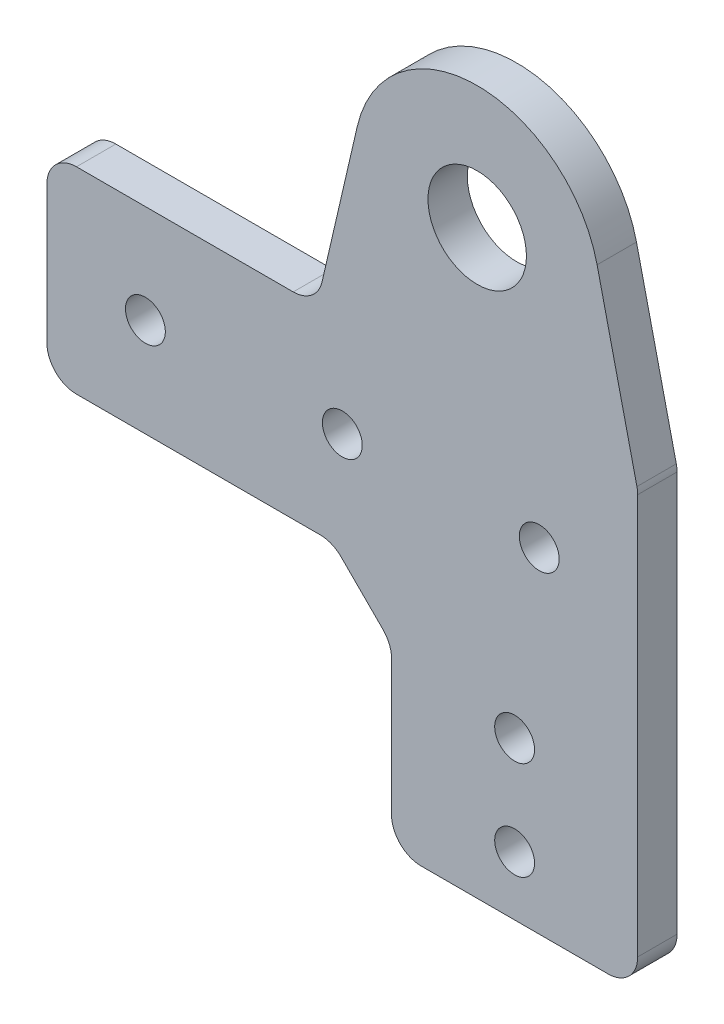
SolidWorks part; units mm, degrees
material "Thornel Mat VMA"
ref_plane "前视基准面" through (0, 0, 0) normal (0, 0, 1) x (1, 0, 0)
ref_plane "上视基准面" through (0, 0, 0) normal (0, 1, 0) x (1, 0, 0)
ref_plane "右视基准面" through (0, 0, 0) normal (1, 0, 0) x (0, 0, -1)
other "Configuration Table"
sketch "草图1" plane through (0, 0, 0) normal (0, 0, 1) x (1, 0, 0)
  line L0 (-35, 0) -> (0, 0)
  line L1 (0, 0) -> (0, -30)
  line L2 (0, -30) -> (25, -30)
  line L3 (25, -30) -> (25, 20)
  line L4 (25, 20) -> (-35, 20)
  line L5 (-35, 20) -> (-35, 0)
  dimension "D1" = 25
  dimension "D2" = 50
  dimension "D3" = 20
  dimension "D4" = 60
extrude "凸台-拉伸1" add sketch "草图1" along normal blind 4
sketch "草图2" plane through (0, 0, 0) normal (0, 0, -1) x (-1, 0, 0)
  line L0 (-15.3472, 38.4733) -> (-25, 20)
  line L1 (-25, -30) -> (-25, 20) construction
  line L2 (-8.7, 35) -> (-8.7, 20) construction
  line L3 (-2.0528, 38.4733) -> (7.6, 20)
  line L4 (-25, 20) -> (35, 20) construction
  line L5 (-25, 20) -> (7.6, 20)
  line L6 (-25, -30) -> (-25, 20) construction
  arc A0 (-2.0528, 38.4733) -> (-15.3472, 38.4733) centre (-8.7, 35) ccw
  dimension "D1" = 15
extrude "凸台-拉伸2" add sketch "草图2" against normal up to surface (4 mm away) up to face at (-3.3333, -3.3333, 4)
sketch "草图3" plane through (0, 0, 0) normal (0, 0, -1) x (-1, 0, 0)
  circle A0 centre (-8.7, 35) radius 5
  dimension "D1" = 10
extrude "切除-拉伸1" cut sketch "草图3" against normal up to surface (4 mm away) up to face at (-1.1333, 8.997, 4)
sketch "草图6" plane through (0, 0, 0) normal (0, 0, -1) x (-1, 0, 0)
  line L0 (-25, -30) -> (-25, 20) construction
  line L1 (-25, -24) -> (0, -24)
  line L2 (-25, -24) -> (-25, -30)
  line L3 (-25, -30) -> (0, -30)
  line L4 (0, -24) -> (0, -30)
  line L5 (0, -7.5) -> (0, -407.5) construction
  line L6 (0, -30) -> (-25, -30) construction
  dimension "D1" = 6
extrude "切除-拉伸4" cut sketch "草图6" against normal through all both and the other way through all
sketch "草图7" plane through (0, 0, 0) normal (0, 0, -1) x (-1, 0, 0)
  line L0 (35, 0) -> (0, 0) construction
  line L1 (-17.5, -18) -> (-7.5, -18) construction
  line L2 (-17.5, -18) -> (-17.5, -8) construction
  line L3 (-17.5, -8) -> (-7.5, -8) construction
  line L4 (-7.5, -18) -> (-7.5, -8) construction
  line L5 (-17.5, -18) -> (-7.5, -8) construction
  line L6 (-17.5, -8) -> (-7.5, -18) construction
  line L7 (-12.5, -24) -> (-12.5, -13) construction
  line L8 (-25, -24) -> (0, -24) construction
  circle A4 centre (-12.5, -8) radius 2.025
  circle A5 centre (-12.5, -18) radius 2.025
  point P0 (-12.5, -13)
  dimension "D4" = 4.05
  dimension "D1" = 10
  dimension "D2" = 10
  dimension "D3" = 8
extrude "切除-拉伸5" cut sketch "草图7" against normal through all both
sketch "草图9" plane through (0, 0, 0) normal (0, 0, -1) x (-1, 0, 0)
  line L0 (-20.8784, 37.8172) -> (-25, 20)
  line L1 (3.4784, 37.8172) -> (7.6, 20)
  line L2 (-25, 20) -> (7.6, 20)
  arc A0 (3.4784, 37.8172) -> (-20.8784, 37.8172) centre (-8.7, 35) ccw
  circle A1 centre (-8.7, 35) radius 5
  dimension "D1" = 25
  dimension "D2" = 10
extrude "凸台-拉伸3" add sketch "草图9" against normal up to surface (4 mm away) up to face at (10.475, -8, 4)
sketch "草图12" plane through (0, 0, 0) normal (0, 0, -1) x (-1, 0, 0)
  line L0 (35, 20) -> (35, 0) construction
  line L1 (-25, -24) -> (-25, 20) construction
  circle A0 centre (-15, 10) radius 2.025
  circle A1 centre (5, 10) radius 2.025
  circle A2 centre (25, 10) radius 2.025
  point P8 (35, 10)
  dimension "D1" = 4.05
  dimension "D2" = 10
  dimension "D3" = 20
  dimension "D4" = 20
extrude "切除-拉伸8" cut sketch "草图12" against normal through all both
sketch "草图13" plane through (0, 0, 0) normal (0, 0, -1) x (-1, 0, 0)
  line L0 (0, -6) -> (6, 0)
  line L1 (0, 0) -> (0, -24) construction
  line L2 (35, 0) -> (0, 0) construction
  line L3 (6, 0) -> (0, 0)
  line L4 (0, 0) -> (0, -6)
  dimension "D1" = 6
  dimension "D2" = 6
extrude "凸台-拉伸4" add sketch "草图13" against normal up to surface (4 mm away) up to face at (12.975, 10, 4)
fillet "圆角1" radius 3 8 edges at (25, -24, 2) (0, -24, 2) (0, -6, 2) (-35, 0, 2) (-35, 20, 2) (-7.6, 20, 2) (25, 20, 2) (-6, 0, 2)
